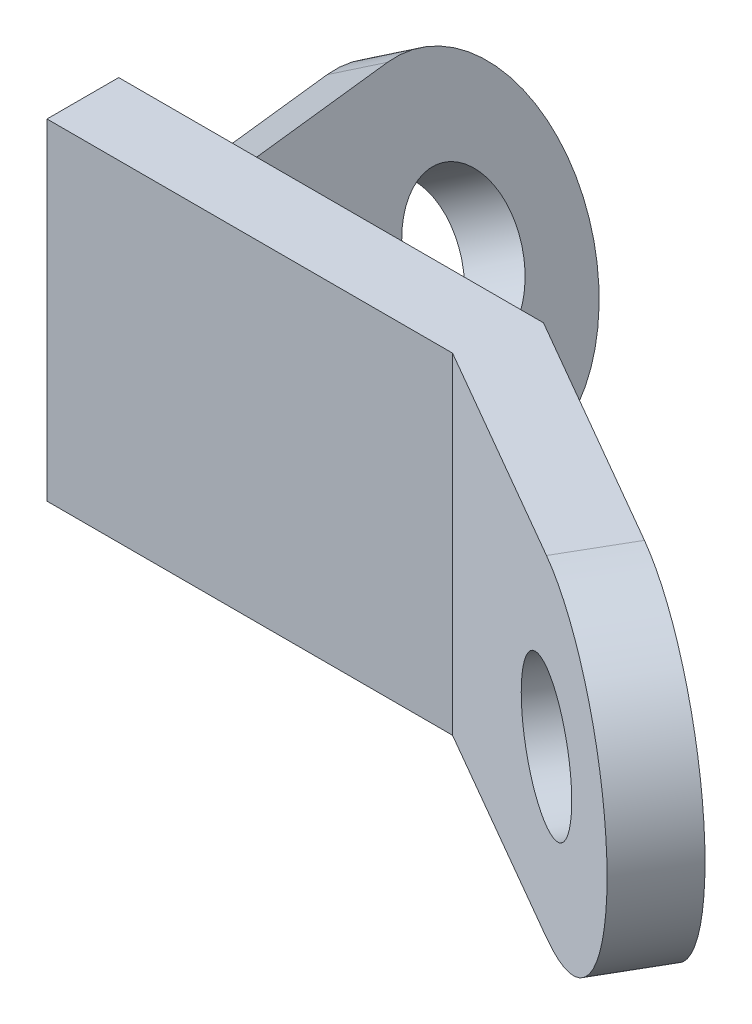
SolidWorks part; units mm, degrees
ref_plane "Front Plane" through (0, 0, 0) normal (0, 0, 1) x (1, 0, 0)
ref_plane "Top Plane" through (0, 0, 0) normal (0, 1, 0) x (1, 0, 0)
ref_plane "Right Plane" through (0, 0, 0) normal (1, 0, 0) x (0, 0, -1)
sketch "Sketch1" plane through (0, 0, 0) normal (0, 1, 0) x (1, 0, 0)
  line L0 (0, 0) -> (75.2583, 0) construction
  line L5 (75.2583, 0) -> (143.032, -39.1292) construction
  line L6 (0, -6.5) -> (73.5167, -6.5)
  line L7 (73.5167, -6.5) -> (139.782, -44.7583)
  line L8 (0, 6.5) -> (77, 6.5)
  line L9 (77, 6.5) -> (146.282, -33.5)
  line L10 (0, -6.5) -> (0, 6.5)
  line L11 (139.782, -44.7583) -> (146.282, -33.5)
  dimension "D1" = 150
  dimension "D2" = 77
  dimension "D3" = 80
  dimension "D4" = 6.5
  dimension "D5" = 6.5
extrude "Boss-Extrude1" add sketch "Sketch1" along normal mid plane 60
sketch "Sketch2" plane through (22.0646, 0, -38.217) normal (0.5, 0, -0.866) x (-0.866, 0, -0.5)
  line L1 (-143.434, 30) -> (-63.434, 30) construction
  line L2 (-143.434, -30) -> (-63.434, -30) construction
  line L3 (-63.434, 30) -> (-63.434, -30) construction
  line L7 (-143.434, -30) -> (-63.434, -30)
  line L8 (-63.434, -30) -> (-63.434, 30)
  line L9 (-63.434, 30) -> (-143.434, 30)
  line L10 (-143.434, 30) -> (-143.434, -30)
  line L11 (-143.434, -30) -> (-113.434, -30)
  line L13 (-113.434, 30) -> (-143.434, 30)
  line L14 (-143.434, 30) -> (-143.434, -30)
  arc A0 (-113.434, 30) -> (-113.434, -30) centre (-113.434, 0) ccw
  circle A1 centre (-113.434, 0) radius 12.5
  line M5 (-143.434, -30) -> (-63.434, -30)
  line M7 (-63.434, 30) -> (-143.434, 30)
  line M8 (-143.434, 30) -> (-143.434, -30)
  dimension "D2" = 25
  dimension "D3" = 50
  dimension "D1" = 0
extrude "Cut-Extrude1" cut sketch "Sketch2" against normal blind 60 contours A1 | A0 M7 M8 | A0 L14 M5
sketch "Sketch3" plane through (0, 0, -6.5) normal (0, 0, -1) x (-1, 0, 0)
  line L0 (-25, 30) -> (-47.2481, -8.5348) construction
  line L1 (-77, 30) -> (0, 30) construction
  line L2 (0, 30) -> (0, -30) construction
  dimension "D1" = 60
  dimension "D2" = 25
ref_plane "Plane1" through (31.0215, 17.9103, -9.5981) normal (0.8365, 0.483, -0.2588) x (0.5, -0.866, 0)
sketch "Sketch4" plane through (31.0215, 17.9103, -9.5981) normal (0.8365, 0.483, -0.2588) x (0.5, -0.866, 0)
  line L1 (-13.4808, -3.2074) -> (41.5192, -3.2074)
  line L2 (-13.4808, -3.2074) -> (-13.4808, 28.7926)
  line L4 (41.5192, -3.2074) -> (41.5192, 28.7926)
  arc A0 (41.5192, 28.7926) -> (-13.4808, 28.7926) centre (14.0192, 28.7926) ccw
  circle A1 centre (14.0192, 28.7926) radius 12.5
  dimension "D3" = 27.5
  dimension "D4" = 25
  dimension "D1" = 55
  dimension "D2" = 32
extrude "Boss-Extrude2" add sketch "Sketch4" against normal blind 10
